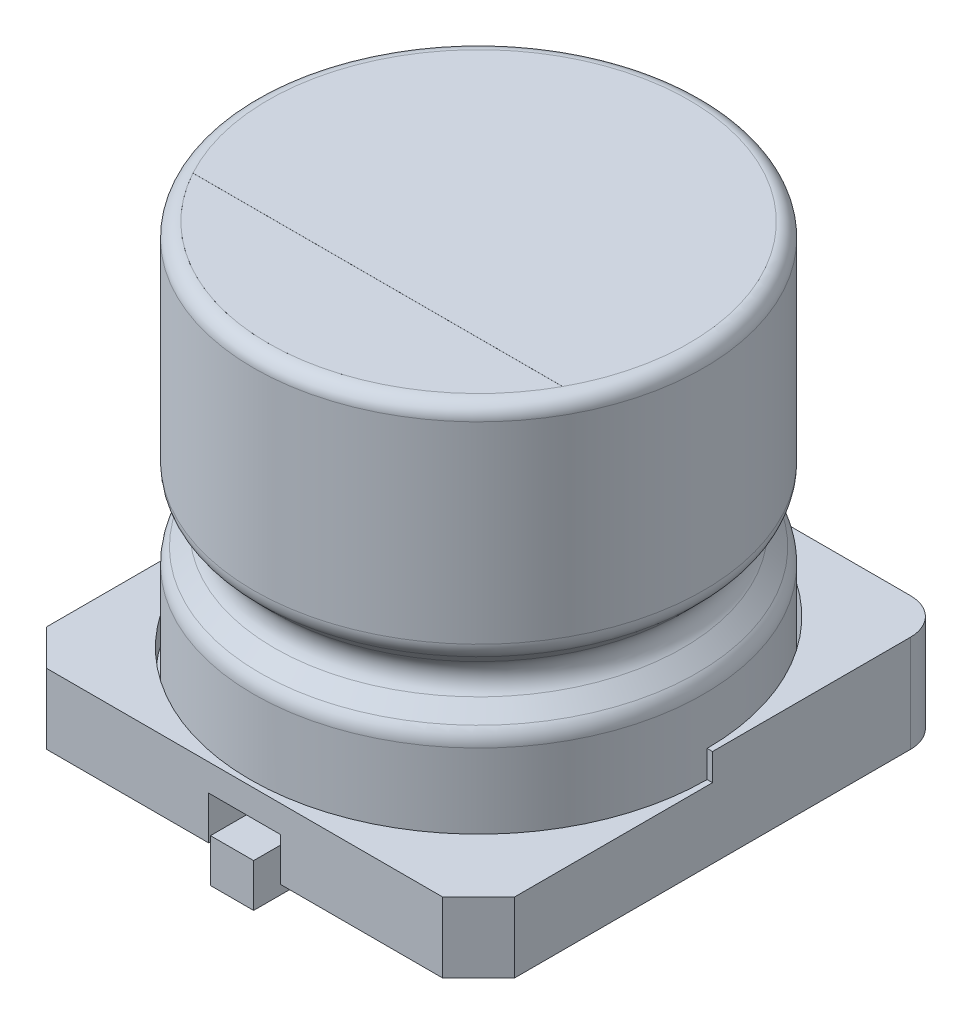
SolidWorks part; units mm, degrees
ref_plane "Front" through (0, 0, 0) normal (0, 0, 1) x (1, 0, 0)
ref_plane "Top" through (0, 0, 0) normal (0, 1, 0) x (1, 0, 0)
ref_plane "Right" through (0, 0, 0) normal (1, 0, 0) x (0, 0, -1)
sketch "Sketch1" plane through (0, 0, 0) normal (0, 0, 1) x (1, 0, 0)
  line L0 (0, 0) -> (-6.25, 0)
  line L1 (50, 0) -> (-50, 0) construction
  line L2 (-6.25, 0) -> (-6.25, 2.7515)
  line L3 (-5.85, 11) -> (0, 11)
  line L4 (0, -50) -> (0, 50) construction
  line L5 (0, 11) -> (0, 0)
  line L6 (-6.0743, 3.1757) -> (-5.6743, 3.5757)
  line L7 (-5.6743, 4.4243) -> (-6.0743, 4.8243)
  line L8 (-6.25, 5.2485) -> (-6.25, 10.6)
  arc A0 (-6.0743, 3.1757) -> (-6.25, 2.7515) centre (-5.65, 2.7515) ccw
  arc A1 (-6.0743, 4.8243) -> (-6.25, 5.2485) centre (-5.65, 5.2485) cw
  arc A2 (-5.6743, 3.5757) -> (-5.6743, 4.4243) centre (-6.0985, 4) ccw
  arc A3 (-6.25, 10.6) -> (-5.85, 11) centre (-5.85, 10.6) cw
  point P16 (-6.25, 5)
  point P19 (-5.25, 4)
  dimension "D5" = 0.6
  dimension "D6" = 0.4
  dimension "D1" = 6.25
  dimension "D2" = 11
  dimension "D3" = 4
  dimension "D4" = 1
revolve "Revolve1" add sketch "Sketch1" angle 360 about L5
sketch "Sketch2" plane through (0, 0, 0) normal (0, -1, 0) x (1, 0, 0)
  line L0 (-6.5, 5.5) -> (-5.5, 6.5)
  line L1 (-5.5, -6.5) -> (-1, -6.5)
  line L2 (-6.5, -5.5) -> (-6.5, 5.5)
  line L3 (-5.5, 6.5) -> (-1, 6.5)
  line L4 (6.5, -5.5) -> (6.5, 5.5)
  line L5 (-6.5, -6.5) -> (6.5, 6.5) construction
  line L6 (-6.5, 6.5) -> (6.5, -6.5) construction
  line L7 (5.5, 6.5) -> (6.5, 5.5)
  line L8 (1, -6.5) -> (5.5, -6.5)
  line L9 (1, 6.5) -> (5.5, 6.5)
  line L10 (-1, 6.5) -> (-1, 1.6)
  line L11 (-1, 1.6) -> (1, 1.6)
  line L12 (1, 6.5) -> (1, 1.6)
  line L13 (-1, -1.6) -> (1, -1.6)
  line L14 (-1, -1.6) -> (-1, -6.5)
  line L16 (1, -1.6) -> (1, -6.5)
  arc A0 (-5.5, -6.5) -> (-6.5, -5.5) centre (-5.5, -5.5) cw
  arc A1 (5.5, -6.5) -> (6.5, -5.5) centre (5.5, -5.5) ccw
  point P0 (0, 0)
  dimension "D3" = 1
  dimension "D1" = 13
  dimension "D2" = 13
  dimension "D4" = 2
  dimension "D5" = 1
  dimension "D8" = 3.2
extrude "Extrude1" add sketch "Sketch2" along normal blind 1.2
sketch "Sketch3" plane through (0, 0, 0) normal (0, 1, 0) x (1, 0, 0)
  line L0 (-1, -6.5) -> (-5.5, -6.5) construction
  line L1 (-5.5, 6.5) -> (-1, 6.5) construction
  line L2 (6.5, 5.5) -> (6.5, -5.5) construction
  line L3 (6.5, -5.5) -> (5.5, -6.5) construction
  line L4 (-5.5, -6.5) -> (-6.5, -5.5) construction
  line L5 (-6.5, -5.5) -> (-6.5, 5.5) construction
  line L6 (5.5, -6.5) -> (-5.5, -6.5)
  line L7 (-5.5, 6.5) -> (5.5, 6.5)
  line L8 (6.5, 5.5) -> (6.5, -5.5)
  line L9 (6.5, -5.5) -> (5.5, -6.5)
  line L10 (-5.5, -6.5) -> (-6.5, -5.5)
  line L11 (-6.5, -5.5) -> (-6.5, 5.5)
  arc A0 (-5.5, 6.5) -> (-6.5, 5.5) centre (-5.5, 5.5) ccw construction
  arc A1 (6.5, 5.5) -> (5.5, 6.5) centre (5.5, 5.5) ccw construction
  arc A2 (-5.5, 6.5) -> (-6.5, 5.5) centre (-5.5, 5.5) ccw
  arc A3 (6.5, 5.5) -> (5.5, 6.5) centre (5.5, 5.5) ccw
  circle A7 centre (0, 0) radius 6.35
  circle A8 centre (0, 0) radius 6.35
  dimension "D1" = 0.5
extrude "Extrude2" add sketch "Sketch3" along normal blind 1.5
sketch "Sketch4" plane through (0, 1.5, 0) normal (0, 1, 0) x (1, 0, 0)
  line L0 (-6.5, 0) -> (-6.35, 0)
  line L1 (6.35, 0) -> (6.5, 0)
  line L6 (-5.5, -6.5) -> (5.5, -6.5)
  line L7 (-6.5, -5.5) -> (-5.5, -6.5)
  line L8 (-6.5, 5.5) -> (-6.5, -5.5)
  line L9 (5.5, 6.5) -> (-5.5, 6.5)
  line L10 (6.5, -5.5) -> (6.5, 5.5)
  line L11 (5.5, -6.5) -> (6.5, -5.5)
  line L12 (-5.5, -6.5) -> (5.5, -6.5)
  line L13 (-6.5, -5.5) -> (-5.5, -6.5)
  line L14 (-6.5, 0) -> (-6.5, -5.5)
  line L16 (6.5, -5.5) -> (6.5, 0)
  line L17 (5.5, -6.5) -> (6.5, -5.5)
  circle A1 centre (0, 0) radius 6.35
  arc A2 (-5.5, 6.5) -> (-6.5, 5.5) centre (-5.5, 5.5) ccw
  arc A3 (6.5, 5.5) -> (5.5, 6.5) centre (5.5, 5.5) ccw
  arc A6 (-6.35, 0) -> (6.35, 0) centre (0, 0) ccw
  dimension "D1" = 0
  dimension "D2" = 0
extrude "Extrude3" cut sketch "Sketch4" against normal blind 0.75
sketch "Sketch5" plane through (0, -1.2, 0) normal (0, -1, 0) x (1, 0, 0)
  line L1 (-4, -4) -> (4, -4) construction
  line L2 (-4, -4) -> (-4, 4) construction
  line L3 (-4, 4) -> (4, 4) construction
  line L4 (4, -4) -> (4, 4) construction
  line L5 (-4, -4) -> (4, 4) construction
  line L6 (-4, 4) -> (4, -4) construction
  circle A0 centre (-4, 4) radius 0.75
  circle A1 centre (4, 4) radius 0.75
  circle A2 centre (-4, -4) radius 0.75
  circle A3 centre (4, -4) radius 0.75
  point P0 (0, 0)
  dimension "D2" = 1.5
  dimension "D1" = 8
extrude "Extrude4" add sketch "Sketch5" along normal blind 0.3
sketch "Sketch6" plane through (0, 0, 0) normal (1, 0, 0) x (0, 0, -1)
  line L0 (2.7, 0) -> (2.7, -0.05)
  line L1 (3.9, -1.25) -> (6.85, -1.25)
  line L2 (0, 50) -> (0, -50) construction
  line L3 (5.5, -1.2) -> (6.5, -1.2) construction
  line L4 (6.1695, 0) -> (1.6, 0) construction
  arc A0 (2.7, -0.05) -> (3.9, -1.25) centre (3.9, -0.05) ccw
  dimension "D4" = 1.2
  dimension "D1" = 6.85
  dimension "D2" = 0.05
  dimension "D3" = 2.7
sketch "Sketch7" plane through (0, 0, 0) normal (0, -1, 0) x (1, 0, 0)
  line L3 (-0.6, -3.3) -> (0.6, -3.3)
  line L4 (-0.6, -3.3) -> (-0.6, -2.1)
  line L5 (-0.6, -2.1) -> (0.6, -2.1)
  line L6 (0.6, -3.3) -> (0.6, -2.1)
  line L7 (-0.6, -3.3) -> (0.6, -2.1) construction
  line L8 (-0.6, -2.1) -> (0.6, -3.3) construction
  line L9 (0, -2.1) -> (0, -3.3) construction
  line L10 (0, -50) -> (0, 50) construction
  line L11 (-0.6, -2.7) -> (0.6, -2.7) construction
  line L12 (50, 0) -> (-50, 0) construction
  dimension "D2" = 2.7
  dimension "D1" = 1.2
sweep "Sweep1" add profiles "Sketch7" path "Sketch6"
mirror "Mirror1" about plane through (0, 0, 0) normal (0, 0, 1) of "Sweep1"
scale "Scale1" scale about centroid uniform scaling yes scale factor 0.5
sketch "Sketch8" plane through (0, 7.809, 0) normal (0, 1, 0) x (1, 0, 0)
  line L0 (-2.5682, -1.3734) -> (2.5682, -1.3734)
  circle A0 centre (0, 0.0266) radius 2.925 construction
  circle A1 centre (0, 0.0266) radius 2.925
  arc A2 (-2.5682, -1.3734) -> (2.5682, -1.3734) centre (0, 0.0266) ccw
  dimension "D2" = 1.4
  dimension "D1" = 0
extrude "Cut-Extrude1" cut sketch "Sketch8" against normal blind 0.001
